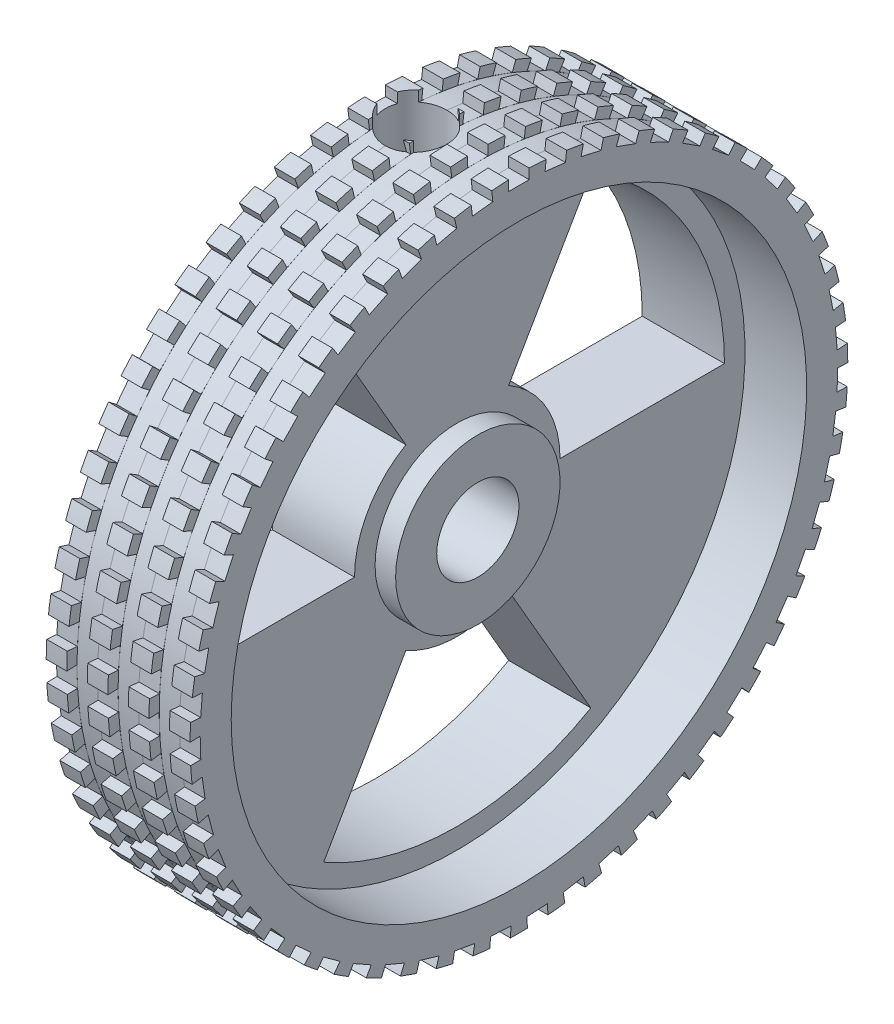
SolidWorks part; units mm, degrees
ref_plane "Front Plane" through (0, 0, 0) normal (0, 0, 1) x (1, 0, 0)
ref_plane "Top Plane" through (0, 0, 0) normal (0, 1, 0) x (1, 0, 0)
ref_plane "Right Plane" through (0, 0, 0) normal (1, 0, 0) x (0, 0, -1)
sketch "Sketch1" plane through (0, 0, 0) normal (0, 1, 0) x (1, 0, 0)
  line L0 (0, 0) -> (8.5938, 0) construction
  line L1 (0, 2) -> (5, 2)
  line L2 (5, 2) -> (5, 4)
  line L3 (5, 4) -> (4, 4)
  line L4 (4, 4) -> (4, 14)
  line L5 (4, 14) -> (7, 14)
  line L6 (7, 14) -> (7, 16)
  line L7 (7, 16) -> (0, 16)
  line L8 (0, 16) -> (0, 2)
  line L10 (0, 0) -> (0, 16) construction
  point P11 (5, 3)
  dimension "D1" = 5
  dimension "D2" = 4
  dimension "D3" = 8
  dimension "D4" = 4
  dimension "D5" = 7
  dimension "D6" = 32
  dimension "D7" = 28
revolve "Revolve1" add sketch "Sketch1" angle 360 about L0
sketch "Sketch2" plane through (0, 0, 0) normal (0, 0, 1) x (1, 0, 0)
  line L0 (0, 16) -> (7, 16) construction
  line L1 (2, 16) -> (2, 0)
  line L2 (2, 0) -> (2.9, 0)
  line L3 (2.9, 0) -> (2.9, 11.5)
  line L4 (2.9, 11.5) -> (3.5, 11.5)
  line L5 (2, 16) -> (3.5, 16)
  line L6 (3.5, 16) -> (3.5, 11.5)
  line L7 (0, 0) -> (7, 0) construction
  line L8 (7, -16) -> (7, 16) construction
  line L9 (0, 0) -> (0, 16) construction
  line L10 (2, 0) -> (2, 19.6613) construction
  line L11 (0, 16) -> (0, -16) construction
  point P15 (0, 15.775)
  point P20 (0, 15.9516)
  dimension "D1" = 4.5
  dimension "D2" = 2
  dimension "D3" = 1.8
  dimension "D4" = 3
revolve "Cut-Revolve1" cut sketch "Sketch2" angle 360 about L10
sketch "Sketch3" plane through (0, 0, 0) normal (0, 0, 1) x (1, 0, 0)
  line L0 (7, 16) -> (3.5, 16) construction
  line L1 (6, 16) -> (5, 16)
  line L2 (6, 16) -> (6, 15.5)
  line L3 (6, 15.5) -> (5, 15.5)
  line L4 (5, 16) -> (5, 15.5)
  line L5 (7, -16) -> (7, 16) construction
  line L7 (0, 0) -> (16.9221, 0) construction
  line L8 (6, 16) -> (5, 16)
  line L9 (6, 16) -> (6, 15.5)
  line L10 (6, 15.5) -> (5, 15.5)
  line L11 (5, 16) -> (5, 15.5)
  dimension "D1" = 1
  dimension "D2" = 0.5
  dimension "D3" = 1
revolve "Cut-Revolve5" cut sketch "Sketch3" angle 360 about L7
sketch "Sketch4" plane through (0, 0, 0) normal (-1, 0, 0) x (0, 0, 1)
  line L0 (0, 16) -> (0, 12.8672) construction
  line L1 (-0.5, 16) -> (0.5, 16)
  line L3 (-0.5, 16) -> (-0.5, 15.5)
  line L5 (0.5, 16) -> (0.5, 15.5)
  line L6 (0.5, 15.5) -> (-0.5, 15.5)
  circle A0 centre (0, 0) radius 16 construction
  point P9 (0, 16)
  dimension "D1" = 1
  dimension "D2" = 0.5
extrude "Cut-Extrude1" cut sketch "Sketch4" against normal blind 10
pattern_linear "LPattern1" count 3 spacing 2 along (-1, 0, 0) of "Cut-Revolve5"
pattern_circular "CirPattern1" count 55 over 360 about axis through (0, 0, 0) along (1, 0, 0) of "Cut-Extrude1"
sketch "Sketch5" plane through (4, 0, 0) normal (1, 0, 0) x (0, 0, -1)
  line L0 (0, 0) -> (0, 5) construction
  line L1 (0, 0) -> (-4.3301, 2.5) construction
  line L2 (-4.3301, 2.5) -> (-11.2583, 6.5)
  line L3 (0, 5) -> (0, 13)
  arc A0 (0, 5) -> (-4.3301, 2.5) centre (0, 0) ccw
  arc A1 (0, 13) -> (-11.2583, 6.5) centre (0, 0) ccw
  dimension "D1" = 60
  dimension "D2" = 5
  dimension "D3" = 5
  dimension "D4" = 8
  dimension "D5" = 8
sketch "Sketch6" plane through (4, 0, 0) normal (1, 0, 0) x (0, 0, -1)
  line L0 (0, 0) -> (2.5, 4.3301) construction
  line L1 (0, 0) -> (0, 5) construction
  line L2 (0, 0) -> (10.4146, 0) construction
  line L3 (6.5, 11.2583) -> (2.5, 4.3301)
  line L4 (13, 0) -> (5, 0)
  circle A0 centre (0, 0) radius 5 construction
  arc A2 (2.5, 4.3301) -> (5, 0) centre (0, 0) cw
  arc A3 (13, 0) -> (6.5, 11.2583) centre (0, 0) ccw
  dimension "D1" = 30
  dimension "D2" = 60
  dimension "D3" = 8
extrude "Cut-Extrude3" cut sketch "Sketch6" against normal blind 10 contours L4 A3 L3 A2
pattern_circular "CirPattern3" count 3 over 360 about axis through (0, 0, 0) along (1, 0, 0) of "Cut-Extrude3"
